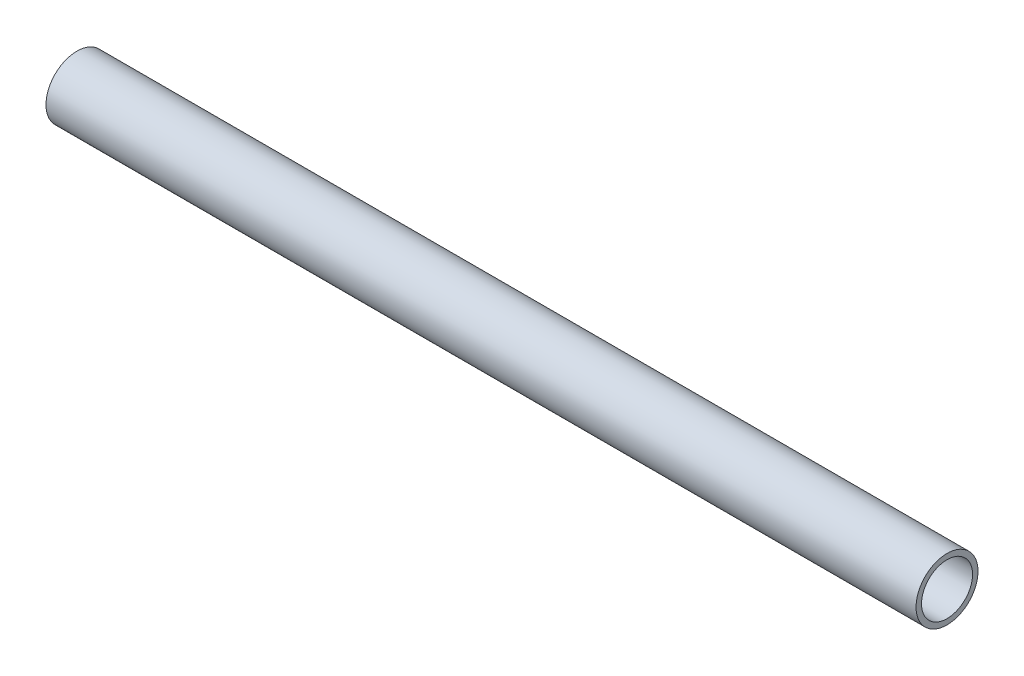
SolidWorks part; units mm, degrees
ref_plane "Front Plane" through (0, 0, 0) normal (0, 0, 1) x (1, 0, 0)
ref_plane "Top Plane" through (0, 0, 0) normal (0, 1, 0) x (1, 0, 0)
ref_plane "Right Plane" through (0, 0, 0) normal (1, 0, 0) x (0, 0, -1)
sketch "Sketch2" plane through (0, 0, 0) normal (0, 0, 1) x (1, 0, 0)
  line L1 (-148.4881, 648.3382) -> (-237.6457, 648.3382)
other "Pipe 0.5 SCH 40(1)"
ref_plane "Plane1" through (-148.4881, 648.3382, 0) normal (-1, 0, 0) x (0, -1, 0)
sketch "Sketch1" plane through (-148.4881, 648.3382, 0) normal (-1, 0, 0) x (0, -1, 0)
  circle A0 centre (0, 0) radius 2.6162
  circle A1 centre (0, 0) radius 3.175
  point P5 (0, 0)
  dimension "In_dia" = 5.2324
  dimension "Out_dia" = 6.35
